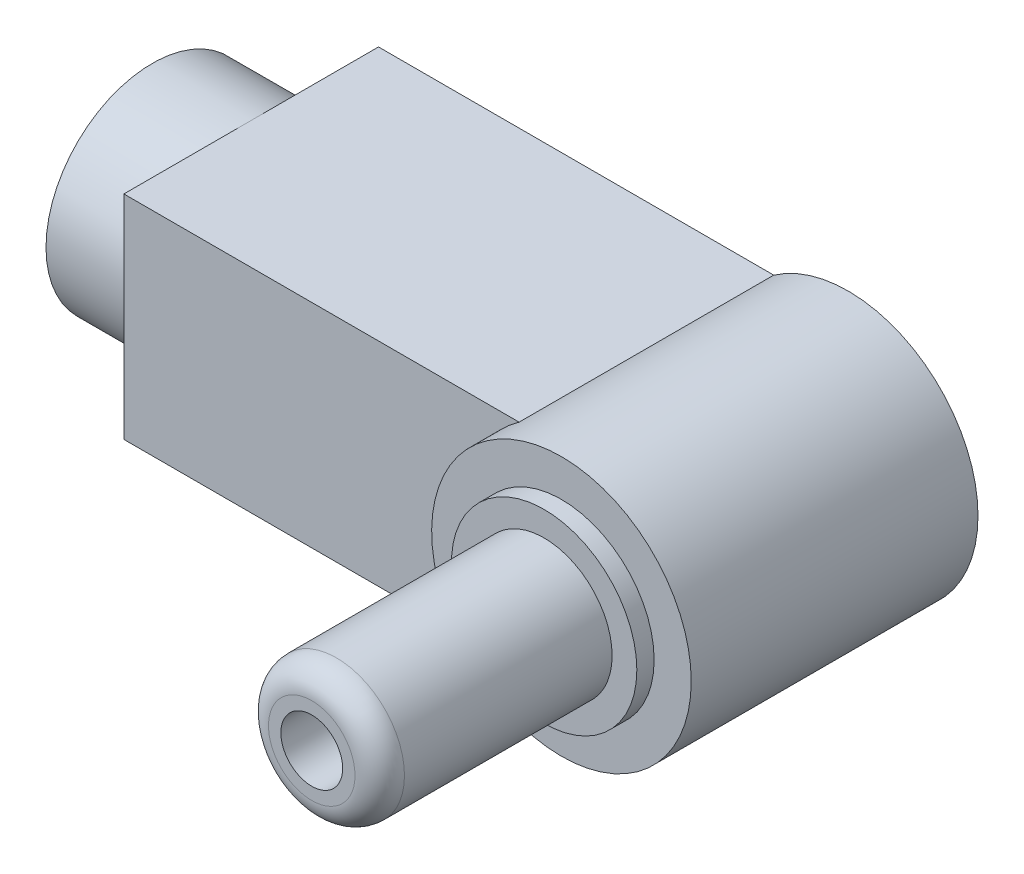
SolidWorks part; units mm, degrees
ref_plane "Front Plane" through (0, 0, 0) normal (0, 0, 1) x (1, 0, 0)
ref_plane "Top Plane" through (0, 0, 0) normal (0, 1, 0) x (1, 0, 0)
ref_plane "Right Plane" through (0, 0, 0) normal (1, 0, 0) x (0, 0, -1)
sketch "Sketch1" plane through (0, 0, 0) normal (0, 0, 1) x (1, 0, 0)
  line L0 (-3.0121, 4.3) -> (-19, 4.3)
  line L1 (-19, 4.3) -> (-19, -4.3)
  line L2 (-19, -4.3) -> (-3.0121, -4.3)
  arc A0 (-3.0121, 4.3) -> (-3.0121, -4.3) centre (0, 0) cw
  dimension "D1" = 5.25
  dimension "D2" = 8.6
  dimension "D3" = 19
extrude "Boss-Extrude1" add sketch "Sketch1" along normal blind 10.3
sketch "Sketch2" plane through (0, 0, 10.3) normal (0, 0, 1) x (1, 0, 0)
  circle A0 centre (0, 0) radius 5.25
extrude "Boss-Extrude2" add sketch "Sketch2" along normal blind 1.3
sketch "Sketch3" plane through (0, 0, 11.6) normal (0, 0, 1) x (1, 0, 0)
  circle A0 centre (0, 0) radius 3.75
  dimension "D1" = 7.5
extrude "Boss-Extrude3" add sketch "Sketch3" along normal blind 0.7
sketch "Sketch4" plane through (0, 0, 12.3) normal (0, 0, 1) x (1, 0, 0)
  circle A0 centre (0, 0) radius 2.75
  circle A1 centre (0, 0) radius 1.25
  dimension "D1" = 5.5
  dimension "D2" = 2.5
extrude "Boss-Extrude4" add sketch "Sketch4" along normal blind 9.4
fillet "Fillet1" radius 1 1 edges at (2.75, 0, 21.7)
sketch "Sketch5" plane through (-19, 0, 0) normal (-1, 0, 0) x (0, 0, 1)
  line L0 (10.3, 4.3) -> (0, 4.3) construction
  line L1 (10.3, -4.3) -> (0, -4.3) construction
  circle A0 centre (5.15, 0) radius 4.3
  circle A1 centre (5.15, 0) radius 2.75
  dimension "D2" = 5.5
  dimension "D1" = 5.15
extrude "Boss-Extrude5" add sketch "Sketch5" along normal blind 4
